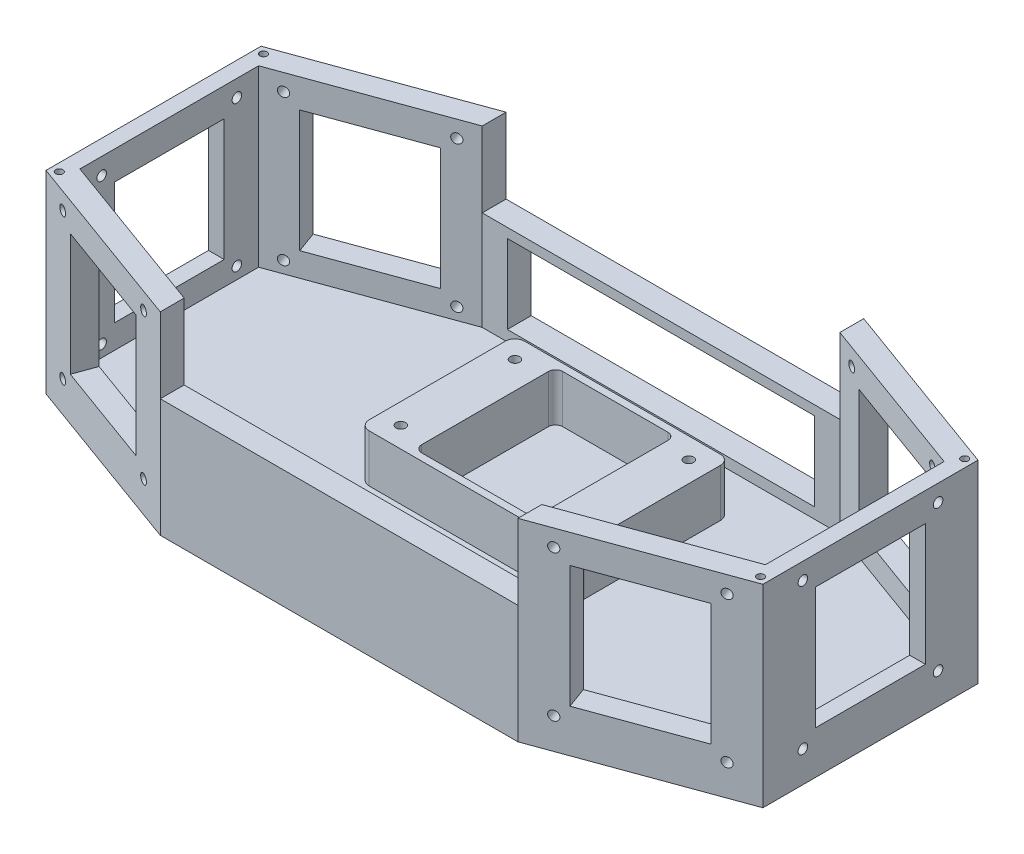
SolidWorks part; units mm, degrees
material "ABS"
ref_plane "Front Plane" through (0, 0, 0) normal (0, 0, 1) x (1, 0, 0)
ref_plane "Top Plane" through (0, 0, 0) normal (0, 1, 0) x (1, 0, 0)
ref_plane "Right Plane" through (0, 0, 0) normal (1, 0, 0) x (0, 0, -1)
sketch "Sketch1" plane through (0, 0, 0) normal (0, 1, 0) x (1, 0, 0)
  line L0 (-150, 0) -> (150, 0) construction
  line L1 (-150, 45) -> (-150, -45)
  line L2 (140.0883, -41.1583) -> (79.948, -63.0476) construction
  line L3 (-140.0883, 41.1583) -> (-142.4825, 47.7362) construction
  line L4 (-140.0883, 41.1583) -> (-79.948, 63.0476) construction
  line L5 (-150, 45) -> (-74.8246, 72.3616)
  line L6 (-79.948, 63.0476) -> (-82.3421, 69.6255) construction
  line L7 (-143, 32) -> (-143, -32) construction
  line L8 (-140.0883, -41.1583) -> (-142.4825, -47.7362) construction
  line L9 (-79.948, -63.0476) -> (-82.3421, -69.6255) construction
  line L10 (-140.0883, -41.1583) -> (-79.948, -63.0476) construction
  line L11 (-150, -45) -> (-74.8246, -72.3616)
  line L12 (0, 74.8501) -> (0, -82.9126) construction
  line L13 (79.948, -63.0476) -> (82.3421, -69.6255) construction
  line L14 (140.0883, -41.1583) -> (142.4825, -47.7362) construction
  line L15 (143, 32) -> (143, -32) construction
  line L16 (79.948, 63.0476) -> (82.3421, 69.6255) construction
  line L17 (140.0883, 41.1583) -> (79.948, 63.0476) construction
  line L18 (140.0883, 41.1583) -> (142.4825, 47.7362) construction
  line L19 (150, -45) -> (74.8246, -72.3616)
  line L20 (150, 45) -> (74.8246, 72.3616)
  line L21 (150, 45) -> (150, -45)
  line L22 (-74.8246, 72.3616) -> (74.8246, 72.3616)
  line L23 (-74.8246, -72.3616) -> (74.8246, -72.3616)
  point P0 (0, 0)
  point P3 (-150, 0)
  point P10 (-143, 0)
  point P13 (0, 0)
  point P37 (143, 0)
  dimension "D1" = 7
  dimension "D2" = 90
  dimension "D3" = 64
  dimension "D4" = 300
  dimension "D5" = 7
  dimension "D6" = 8
  dimension "D7" = 80
  dimension "D8" = 110
extrude "Boss-Extrude1" add sketch "Sketch1" along normal blind 8
sketch "Sketch2" plane through (0, 8, 0) normal (0, 1, 0) x (1, 0, 0)
  line L0 (0, 72.3616) -> (0, -72.3616) construction
  line L1 (74.8246, 72.3616) -> (-74.8246, 72.3616) construction
  line L2 (-74.8246, -72.3616) -> (74.8246, -72.3616) construction
  line L3 (-74.8246, -72.3616) -> (-74.8246, -62.3616) construction
  line L4 (-74.8246, -62.3616) -> (-64.3246, -62.3616) construction
  line L5 (-64.3246, -62.3616) -> (-64.3246, -72.3616) construction
  line L6 (-64.3246, -72.3616) -> (-74.8246, -72.3616) construction
  line L7 (64.3246, -72.3616) -> (74.8246, -72.3616) construction
  line L8 (64.3246, -62.3616) -> (64.3246, -72.3616) construction
  line L9 (74.8246, -62.3616) -> (64.3246, -62.3616) construction
  line L10 (74.8246, -72.3616) -> (74.8246, -62.3616) construction
  line L11 (-150, 0) -> (150, 0) construction
  line L12 (-150, 45) -> (-150, -45) construction
  line L13 (150, -45) -> (150, 45) construction
  line L14 (74.8246, 72.3616) -> (74.8246, 62.3616)
  line L15 (74.8246, 62.3616) -> (64.3246, 62.3616)
  line L16 (64.3246, 62.3616) -> (64.3246, 72.3616)
  line L17 (64.3246, 72.3616) -> (74.8246, 72.3616)
  line L18 (-64.3246, 72.3616) -> (-74.8246, 72.3616)
  line L19 (-64.3246, 62.3616) -> (-64.3246, 72.3616)
  line L20 (-74.8246, 62.3616) -> (-64.3246, 62.3616)
  line L21 (-74.8246, 72.3616) -> (-74.8246, 62.3616)
  dimension "D1" = 10.5
  dimension "D2" = 10
extrude "Boss-Extrude2" add sketch "Sketch2" along normal blind 37.5
sketch "Sketch4" plane through (0, 8, 0) normal (0, 1, 0) x (1, 0, 0)
  line L1 (-64.3246, 72.3616) -> (64.3246, 72.3616)
  line L2 (-64.3246, 72.3616) -> (-64.3246, 62.3616)
  line L3 (-64.3246, 62.3616) -> (64.3246, 62.3616)
  line L4 (64.3246, 72.3616) -> (64.3246, 62.3616)
extrude "Boss-Extrude4" add sketch "Sketch4" along normal blind 4.5
sketch "Sketch5" plane through (0, 8, 0) normal (0, 1, 0) x (1, 0, 0)
  line L0 (-74.8246, 62.3616) -> (-87.0406, 57.9153)
  line L1 (-74.8246, 72.3616) -> (-150, 45) construction
  line L2 (-74.8246, 72.3616) -> (-74.8246, 62.3616)
  line L3 (-74.8246, 72.3616) -> (-150, 45)
  line L4 (-87.0406, 57.9153) -> (-140.6031, 38.4202)
  line L5 (-150, 45) -> (-140.6031, 38.4202) construction
  line L6 (-74.8246, -72.3616) -> (-74.8246, -62.3616)
  line L7 (-140.6031, 38.4202) -> (-143.4222, 37.3941)
  line L8 (-150, 45) -> (-143.4222, 37.3941) construction
  line L9 (-150, 0) -> (-74.8246, 0) construction
  line L10 (-150, 45) -> (-150, -45) construction
  line L11 (-79.6003, 0) -> (86.9407, 0) construction
  line L12 (-124.0599, 0) -> (-121.8599, 0) construction
  line L13 (-74.8246, -62.3616) -> (-87.0406, -57.9153)
  line L14 (-140.6031, -38.4202) -> (-143.4222, -37.3941)
  line L15 (-87.0406, -57.9153) -> (-140.6031, -38.4202)
  line L16 (-150, -45) -> (-143.4222, -37.3941) construction
  line L17 (-74.8246, -72.3616) -> (-150, -45)
  line L18 (-143.4222, 37.3941) -> (-143.4222, -37.3941)
  line L19 (-150, 45) -> (-150, -45)
  line L20 (0, 72.1209) -> (0, -72.3616) construction
  line L21 (-74.8246, -72.3616) -> (74.8246, -72.3616) construction
  line L22 (150, -45) -> (143.4222, -37.3941) construction
  line L23 (150, 0) -> (74.8246, 0) construction
  line L24 (150, 45) -> (143.4222, 37.3941) construction
  line L25 (150, 45) -> (140.6031, 38.4202) construction
  line L26 (150, 45) -> (150, -45)
  line L27 (143.4222, 37.3941) -> (143.4222, -37.3941)
  line L28 (74.8246, -72.3616) -> (150, -45)
  line L29 (87.0406, -57.9153) -> (140.6031, -38.4202)
  line L30 (140.6031, -38.4202) -> (143.4222, -37.3941)
  line L31 (74.8246, -62.3616) -> (87.0406, -57.9153)
  line L32 (140.6031, 38.4202) -> (143.4222, 37.3941)
  line L33 (74.8246, -72.3616) -> (74.8246, -62.3616)
  line L34 (87.0406, 57.9153) -> (140.6031, 38.4202)
  line L35 (74.8246, 72.3616) -> (150, 45)
  line L36 (74.8246, 72.3616) -> (74.8246, 62.3616)
  line L37 (74.8246, 62.3616) -> (87.0406, 57.9153)
  dimension "D1" = 13
  dimension "D2" = 55
  dimension "D3" = 3
extrude "Boss-Extrude5" add sketch "Sketch5" along normal blind 10
sketch "Sketch6" plane through (0, 45.5, 0) normal (0, 1, 0) x (1, 0, 0)
  line L1 (74.8246, 72.3616) -> (-74.8246, 72.3616)
  line L2 (74.8246, 72.3616) -> (74.8246, 62.3616)
  line L3 (74.8246, 62.3616) -> (-74.8246, 62.3616)
  line L4 (-74.8246, 72.3616) -> (-74.8246, 62.3616)
extrude "Boss-Extrude6" add sketch "Sketch6" along normal blind 4
sketch "Sketch7" plane through (32.0094, 0, -87.9451) normal (0.342, 0, -0.9397) x (-0.9397, 0, -0.342)
  line L0 (-85.563, 18) -> (-85.563, 0) construction
  line L1 (-125.563, 18) -> (-45.563, 18) construction
  line L2 (-125.563, 0) -> (-45.563, 0) construction
  line L3 (-113.853, 13) -> (-85.563, 13) construction
  circle A0 centre (-113.853, 13) radius 2
  circle A1 centre (-57.273, 13) radius 2
  dimension "D1" = 56.58
  dimension "D2" = 4
  dimension "D3" = 5
extrude "Cut-Extrude1" cut sketch "Sketch7" against normal up to next (9.3969 mm away)
ref_plane "Plane1" through (0, 0, 0) normal (1, 0, 0) x (0, 0, -1)
mirror "Mirror1" about plane through (0, 0, 0) normal (1, 0, 0) of "Cut-Extrude1"
ref_plane "Plane2" through (0, 0, 0) normal (0, 0, -1) x (-1, 0, 0)
mirror "Mirror2" about plane through (0, 0, 0) normal (0, 0, -1) of "Cut-Extrude1", "Mirror1"
sketch "Sketch8" plane through (150, 0, 0) normal (1, 0, 0) x (0, 0, -1)
  line L0 (0, 18) -> (0, 0) construction
  line L1 (-45, 18) -> (45, 18) construction
  line L2 (-28.29, 13) -> (28.29, 13) construction
  line L3 (0, -27.225) -> (0, 27.225) construction
  circle A0 centre (-28.29, 13) radius 2
  circle A1 centre (28.29, 13) radius 2
  point P8 (0, 13)
  dimension "D1" = 56.58
  dimension "D3" = 4
  dimension "D2" = 5
extrude "Cut-Extrude2" cut sketch "Sketch8" against normal up to next (75.1754 mm away)
mirror "Mirror3" about plane through (0, 0, 0) normal (1, 0, 0) of "Cut-Extrude2"
sketch "Sketch9" plane through (0, 18, 0) normal (0, 1, 0) x (1, 0, 0)
  line L0 (143.4222, 23) -> (150, 23)
  line L1 (143.4222, 37.3941) -> (143.4222, -37.3941) construction
  line L2 (150, -45) -> (150, 45) construction
  line L3 (150, 23) -> (150, 45)
  line L4 (150, 45) -> (134.0252, 50.8143)
  line L5 (150, 45) -> (74.8246, 72.3616) construction
  line L6 (134.0252, 50.8143) -> (130.8113, 41.9841)
  line L7 (74.8246, 62.3616) -> (143.4222, 37.3941) construction
  line L8 (130.8113, 41.9841) -> (143.4222, 37.3941)
  line L9 (143.4222, 37.3941) -> (143.4222, 23)
  line L12 (74.8246, 72.3616) -> (90.7994, 66.5473)
  line L13 (90.7994, 66.5473) -> (87.5854, 57.717)
  line L14 (87.5854, 57.717) -> (74.8246, 62.3616)
  line L15 (74.8246, 72.3616) -> (74.8246, 62.3616) construction
  line L16 (74.8246, 62.3616) -> (74.8246, 72.3616)
  line L17 (0, -70.7131) -> (0, 92.4677) construction
  line L18 (-74.8246, 62.3616) -> (-74.8246, 72.3616)
  line L19 (-87.5854, 57.717) -> (-74.8246, 62.3616)
  line L20 (-90.7994, 66.5473) -> (-87.5854, 57.717)
  line L21 (-74.8246, 72.3616) -> (-90.7994, 66.5473)
  line L22 (-143.4222, 37.3941) -> (-143.4222, 23)
  line L23 (-130.8113, 41.9841) -> (-143.4222, 37.3941)
  line L24 (-134.0252, 50.8143) -> (-130.8113, 41.9841)
  line L25 (-150, 45) -> (-134.0252, 50.8143)
  line L26 (-150, 23) -> (-150, 45)
  line L27 (-143.4222, 23) -> (-150, 23)
  line L28 (150, 0) -> (-150, 0) construction
  line L29 (-150, 45) -> (-150, -45) construction
  line L30 (143.4222, -37.3941) -> (143.4222, -23)
  line L31 (130.8113, -41.9841) -> (143.4222, -37.3941)
  line L32 (134.0252, -50.8143) -> (130.8113, -41.9841)
  line L33 (150, -45) -> (134.0252, -50.8143)
  line L34 (150, -23) -> (150, -45)
  line L35 (143.4222, -23) -> (150, -23)
  line L36 (-143.4222, -23) -> (-150, -23)
  line L37 (-150, -23) -> (-150, -45)
  line L38 (-150, -45) -> (-134.0252, -50.8143)
  line L39 (-134.0252, -50.8143) -> (-130.8113, -41.9841)
  line L40 (-130.8113, -41.9841) -> (-143.4222, -37.3941)
  line L41 (-143.4222, -37.3941) -> (-143.4222, -23)
  line L42 (-74.8246, -72.3616) -> (-90.7994, -66.5473)
  line L43 (-90.7994, -66.5473) -> (-87.5854, -57.717)
  line L44 (-87.5854, -57.717) -> (-74.8246, -62.3616)
  line L45 (-74.8246, -62.3616) -> (-74.8246, -72.3616)
  line L46 (74.8246, -62.3616) -> (74.8246, -72.3616)
  line L47 (87.5854, -57.717) -> (74.8246, -62.3616)
  line L48 (90.7994, -66.5473) -> (87.5854, -57.717)
  line L49 (74.8246, -72.3616) -> (90.7994, -66.5473)
  dimension "D1" = 22
  dimension "D2" = 17
  dimension "D3" = 17
extrude "Boss-Extrude8" add sketch "Sketch9" along normal blind 63
sketch "Sketch10" plane through (32.0094, 0, -87.9451) normal (0.342, 0, -0.9397) x (-0.9397, 0, -0.342)
  line L0 (-85.563, 0) -> (-85.563, 86.9159) construction
  line L1 (-125.563, 0) -> (-45.563, 0) construction
  line L2 (-113.853, 13) -> (-113.853, 74) construction
  circle A0 centre (-113.853, 74) radius 2
  circle A1 centre (-113.853, 13) radius 2 construction
  circle A2 centre (-57.273, 74) radius 2
  dimension "D1" = 61
extrude "Cut-Extrude3" cut sketch "Sketch10" against normal up to next (9.3969 mm away)
mirror "Mirror4" about plane through (0, 0, 0) normal (1, 0, 0) of "Cut-Extrude3"
mirror "Mirror5" about plane through (0, 0, 0) normal (0, 0, -1) of "Cut-Extrude3", "Mirror4"
sketch "Sketch11" plane through (150, 0, 0) normal (1, 0, 0) x (0, 0, -1)
  line L0 (-28.29, 13) -> (-28.29, 74) construction
  line L1 (0, 18) -> (0, 79.1024) construction
  line L2 (-23, 18) -> (23, 18) construction
  circle A0 centre (-28.29, 74) radius 2
  circle A1 centre (-28.29, 13) radius 2 construction
  circle A2 centre (28.29, 74) radius 2
  dimension "D1" = 61
extrude "Cut-Extrude4" cut sketch "Sketch11" against normal up to next (75.1754 mm away)
mirror "Mirror6" about plane through (0, 0, 0) normal (1, 0, 0) of "Cut-Extrude4"
sketch "Sketch12" plane through (0, 81, 0) normal (0, 1, 0) x (1, 0, 0)
  line L0 (130.8113, 41.9841) -> (87.5854, 57.717)
  line L1 (87.5854, 57.717) -> (90.7994, 66.5473)
  line L2 (90.7994, 66.5473) -> (134.0252, 50.8143)
  line L3 (134.0252, 50.8143) -> (130.8113, 41.9841)
  line L4 (0, 103.9036) -> (0, -116.4859) construction
  line L5 (143.4222, 23) -> (150, 23)
  line L6 (143.4222, 23) -> (143.4222, -23)
  line L7 (143.4222, -23) -> (150, -23)
  line L8 (150, 23) -> (150, -23)
  line L9 (150, 0) -> (-150, 0) construction
  line L10 (-150, 23) -> (-150, -23) construction
  line L11 (134.0252, -50.8143) -> (130.8113, -41.9841)
  line L12 (90.7994, -66.5473) -> (134.0252, -50.8143)
  line L13 (87.5854, -57.717) -> (90.7994, -66.5473)
  line L14 (130.8113, -41.9841) -> (87.5854, -57.717)
  line L15 (-130.8113, -41.9841) -> (-87.5854, -57.717)
  line L16 (-87.5854, -57.717) -> (-90.7994, -66.5473)
  line L17 (-90.7994, -66.5473) -> (-134.0252, -50.8143)
  line L18 (-134.0252, -50.8143) -> (-130.8113, -41.9841)
  line L19 (-150, 23) -> (-150, -23)
  line L20 (-143.4222, -23) -> (-150, -23)
  line L21 (-143.4222, 23) -> (-143.4222, -23)
  line L22 (-143.4222, 23) -> (-150, 23)
  line L23 (-134.0252, 50.8143) -> (-130.8113, 41.9841)
  line L24 (-90.7994, 66.5473) -> (-134.0252, 50.8143)
  line L25 (-87.5854, 57.717) -> (-90.7994, 66.5473)
  line L26 (-130.8113, 41.9841) -> (-87.5854, 57.717)
extrude "Boss-Extrude9" add sketch "Sketch12" against normal blind 12
sketch "Sketch13" plane through (0, 8, 0) normal (0, 1, 0) x (1, 0, 0)
  line L0 (0, 62.3616) -> (0, -72.3616) construction
  line L1 (-41, 46.2316) -> (-29, 46.2316)
  line L2 (-45, 42.2316) -> (-45, -14.7684)
  line L3 (-41, -18.7684) -> (-29, -18.7684)
  line L4 (45, 42.2316) -> (45, -14.7684)
  line L5 (-74.8246, 62.3616) -> (74.8246, 62.3616) construction
  line L6 (-74.8246, -72.3616) -> (74.8246, -72.3616) construction
  line L7 (-25, 40.2316) -> (-25, -12.7684)
  line L8 (25, 40.2316) -> (25, -12.7684)
  line L9 (29, 46.2316) -> (41, 46.2316)
  line L10 (29, -18.7684) -> (41, -18.7684)
  line L11 (-25, 46.2316) -> (25, 46.2316) construction
  line L12 (-25, -18.7684) -> (25, -18.7684) construction
  line L13 (-29, 46.2316) -> (29, 46.2316)
  line L14 (-22, 43.2316) -> (22, 43.2316)
  line L15 (-22, -15.7684) -> (22, -15.7684)
  line L16 (-29, -18.7684) -> (29, -18.7684)
  arc A0 (-45, -14.7684) -> (-41, -18.7684) centre (-41, -14.7684) ccw
  arc A1 (41, -18.7684) -> (45, -14.7684) centre (41, -14.7684) ccw
  arc A2 (41, 46.2316) -> (45, 42.2316) centre (41, 42.2316) cw
  arc A3 (-41, 46.2316) -> (-45, 42.2316) centre (-41, 42.2316) ccw
  arc A4 (-25, -12.7684) -> (-22, -15.7684) centre (-22, -12.7684) ccw
  arc A5 (25, -12.7684) -> (22, -15.7684) centre (22, -12.7684) cw
  arc A6 (25, 40.2316) -> (22, 43.2316) centre (22, 40.2316) ccw
  arc A7 (-25, 40.2316) -> (-22, 43.2316) centre (-22, 40.2316) cw
  point P10 (0, 46.2316)
  point P15 (45, -18.7684)
  point P18 (45, 46.2316)
  point P21 (-45, 46.2316)
  dimension "D4" = 4
  dimension "D7" = 3
  dimension "D9" = 3
  dimension "D1" = 65
  dimension "D2" = 90
  dimension "D3" = 16.13
  dimension "D5" = 20
  dimension "D6" = 25
  dimension "D8" = 3
extrude "Boss-Extrude10" add sketch "Sketch13" along normal blind 20
sketch "Sketch14" plane through (0, 28, 0) normal (0, 1, 0) x (1, 0, 0)
  line L0 (-45, 42.2316) -> (-45, -14.7684) construction
  line L1 (-36.37, 37.6066) -> (-36.37, -10.1434) construction
  line L2 (-45, 13.7316) -> (-25, 13.7316) construction
  line L3 (-25, -12.7684) -> (-25, 40.2316) construction
  circle A0 centre (-36.37, 37.6066) radius 2
  circle A1 centre (-36.37, -10.1434) radius 2
  point P10 (-36.37, 13.7316)
  dimension "D1" = 4
  dimension "D2" = 47.75
  dimension "D3" = 8.63
extrude "Cut-Extrude5" cut sketch "Sketch14" against normal blind 10
mirror "Mirror7" about plane through (0, 0, 0) normal (1, 0, 0) of "Cut-Extrude5"
sketch "Sketch15" plane through (0, 8, 0) normal (0, 1, 0) x (1, 0, 0)
  line L1 (-74.8246, -72.3616) -> (74.8246, -72.3616)
  line L2 (-74.8246, -72.3616) -> (-74.8246, -62.3616)
  line L3 (-74.8246, -62.3616) -> (74.8246, -62.3616)
  line L4 (74.8246, -72.3616) -> (74.8246, -62.3616)
extrude "Boss-Extrude11" add sketch "Sketch15" along normal blind 41.5
sketch "Sketch16" plane through (0, 0, -72.3616) normal (0, 0, -1) x (-1, 0, 0)
  line L0 (-74.8246, 81) -> (-47.5, 81)
  line L1 (0, 0) -> (0, 104.0722) construction
  line L2 (0, 44.55) -> (0, -44.55) construction
  line L3 (74.8246, 81) -> (47.5, 81)
  line L4 (-74.8246, 49.5) -> (74.8246, 49.5) construction
  line L5 (-74.8246, 81) -> (-74.8246, 49.5)
  line L6 (-74.8246, 49.5) -> (74.8246, 49.5)
  line L7 (74.8246, 49.5) -> (74.8246, 81)
  arc A0 (-47.5, 81) -> (47.5, 81) centre (0, 101.0635) ccw
  dimension "D1" = 95
sketch "Sketch17" plane through (0, 81, 0) normal (0, 1, 0) x (1, 0, 0)
  line L0 (150, -45) -> (123.1193, -26.178) construction
  line L1 (150, 0) -> (-150, 0) construction
  line L2 (150, -45) -> (150, 45) construction
  line L3 (-150, 45) -> (-150, -45) construction
  line L4 (0, 76.5626) -> (0, -108.8084) construction
  circle A0 centre (146.7234, -42.7057) radius 1.5
  circle A1 centre (146.7234, 42.7057) radius 1.5
  circle A2 centre (-146.7234, 42.7057) radius 1.5
  circle A3 centre (-146.7234, -42.7057) radius 1.5
  dimension "D2" = 3
  dimension "D1" = 55
  dimension "D3" = 4
extrude "Cut-Extrude6" cut sketch "Sketch17" against normal blind 10
